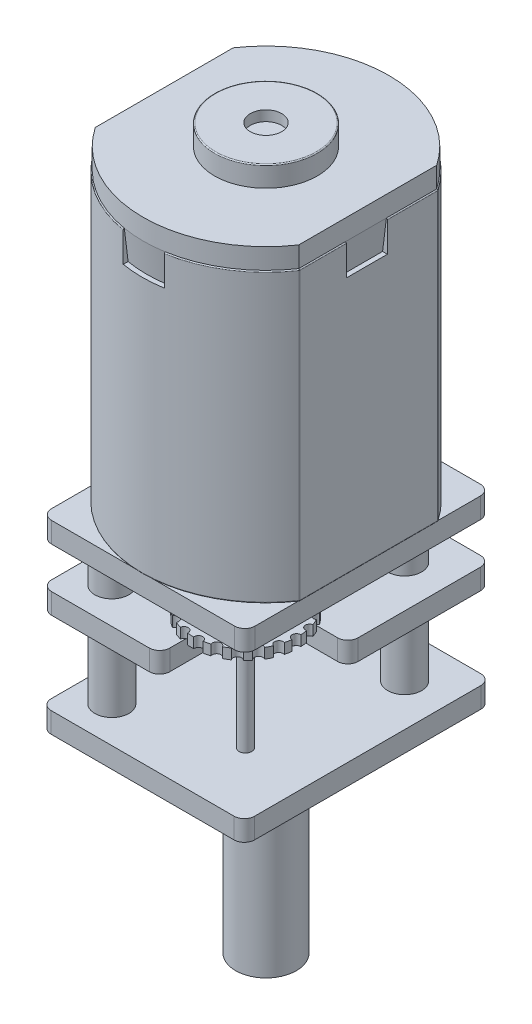
SolidWorks part; units mm, degrees
ref_plane "Front Plane" through (0, 0, 0) normal (0, 0, 1) x (1, 0, 0)
ref_plane "Top Plane" through (0, 0, 0) normal (0, 1, 0) x (1, 0, 0)
ref_plane "Right Plane" through (0, 0, 0) normal (1, 0, 0) x (0, 0, -1)
sketch "Sketch1" plane through (0, 0, 0) normal (0, 1, 0) x (1, 0, 0)
  line L2 (-5, -3.3706) -> (-5, 3.3706)
  line L4 (5, -3.3706) -> (5, 3.3706)
  line L5 (-3.051, -5.2012) -> (3.051, 5.2012) construction
  line L6 (-3.051, 5.2012) -> (3.051, -5.2012) construction
  arc A0 (-5, -3.3706) -> (5, -3.3706) centre (0, 0) ccw
  arc A1 (5, 3.3706) -> (-5, 3.3706) centre (0, 0) ccw
  dimension "D1" = 12.06
extrude "Boss-Extrude1" add sketch "Sketch1" along normal blind 14
fillet "Fillet2" radius 0.05 12 edges at (-5, 7, 3.3706) (5, 7, 3.3706) (5, 7, -3.3706) (-5, 7, -3.3706) (-5, 0, 0) (0, 0, -6.03) (5, 0, 0) (0, 0, 6.03) (-5, 14, 0) (0, 14, -6.03) (5, 14, 0) (0, 14, 6.03)
sketch "Sketch2" plane through (0, 14, 0) normal (0, 1, 0) x (1, 0, 0)
  line L1 (1, 7.8898) -> (-1, 7.8898)
  line L2 (1, 7.8898) -> (1, -7.8898)
  line L3 (1, -7.8898) -> (-1, -7.8898)
  line L4 (-1, 7.8898) -> (-1, -7.8898)
  line L5 (1, 7.8898) -> (-1, -7.8898) construction
  line L6 (1, -7.8898) -> (-1, 7.8898) construction
  line L7 (6.96, 0.9081) -> (0, 0.9081)
  line L8 (6.96, 0.9081) -> (6.96, -1.0919)
  line L9 (6.96, -1.0919) -> (0, -1.0919)
  line L10 (0, 0.9081) -> (0, -1.0919)
  line L11 (6.96, 0.9081) -> (0, -1.0919) construction
  line L12 (6.96, -1.0919) -> (0, 0.9081) construction
  point P0 (0, 0)
  point P6 (3.48, -0.0919)
  dimension "D1" = 2
  dimension "D2" = 2
extrude "Cut-Extrude1" cut sketch "Sketch2" against normal blind 1.5 contours L2 L3 L4 L1 | L7 L10 L9 L8
sketch "Sketch3" plane through (0, 14, 0) normal (0, 1, 0) x (1, 0, 0)
  line L0 (4.95, 3.3553) -> (4.95, -3.3553)
  line L1 (-4.95, 3.3553) -> (-4.95, -3.3553)
  arc A0 (4.95, -3.3553) -> (-4.95, -3.3553) centre (0, 0) cw
  arc A1 (4.95, 3.3553) -> (-4.95, 3.3553) centre (0, 0) ccw
extrude "Boss-Extrude2" add sketch "Sketch3" along normal blind 1 and the other way blind 1.5 draft 7
sketch "Sketch4" plane through (0, 15, 0) normal (0, 1, 0) x (1, 0, 0)
  circle A0 centre (0, 0) radius 2.5
  dimension "D1" = 5
extrude "Boss-Extrude3" add sketch "Sketch4" along normal blind 1
fillet "Fillet3" radius 0.05 1 edges at (0, 16, 2.5)
sketch "Sketch5" plane through (0, 16, 0) normal (0, 1, 0) x (1, 0, 0)
  circle A0 centre (0, 0) radius 0.7637
extrude "Cut-Extrude2" cut sketch "Sketch5" against normal blind 0.5
sketch "Sketch6" plane through (0, 0, 0) normal (0, -1, 0) x (-1, 0, 0)
  line L1 (-4.45, -5.98) -> (4.45, -5.98)
  line L2 (-4.95, -5.48) -> (-4.95, 5.48)
  line L3 (-4.45, 5.98) -> (4.45, 5.98)
  line L4 (4.95, -5.48) -> (4.95, 5.48)
  line L5 (-4.95, -5.98) -> (4.95, 5.98) construction
  line L6 (-4.95, 5.98) -> (4.95, -5.98) construction
  arc A0 (-4.95, 5.48) -> (-4.45, 5.98) centre (-4.45, 5.48) cw
  arc A1 (4.45, 5.98) -> (4.95, 5.48) centre (4.45, 5.48) cw
  arc A2 (4.45, -5.98) -> (4.95, -5.48) centre (4.45, -5.48) ccw
  arc A3 (-4.45, -5.98) -> (-4.95, -5.48) centre (-4.45, -5.48) cw
  point P0 (0, 0)
  dimension "D1" = 0.5
extrude "Boss-Extrude4" add sketch "Sketch6" along normal blind 1
sketch "Sketch7" plane through (0, -1, 0) normal (0, -1, 0) x (1, 0, 0)
  line L0 (-4.8036, -5.8336) -> (4.8036, 5.8336) construction
  circle A0 centre (2.8963, -3.8498) radius 0.8279
  arc A1 (-4.95, -5.48) -> (-4.45, -5.98) centre (-4.45, -5.48) ccw construction
  arc A2 (4.95, 5.48) -> (4.45, 5.98) centre (4.45, 5.48) ccw construction
  circle A3 centre (-3.2633, 4.2361) radius 0.8279
extrude "Boss-Extrude5" add sketch "Sketch7" along normal blind 2
sketch "Sketch8" plane through (0, -3, 0) normal (0, -1, 0) x (1, 0, 0)
  line L1 (0.2998, 5.98) -> (-4.45, 5.98)
  line L2 (4.95, 0.4662) -> (4.95, -5.48)
  line L3 (4.45, -5.98) -> (-4.45, -5.98)
  line L4 (-4.95, 5.48) -> (-4.95, -5.48)
  line L5 (0.7998, 0.9662) -> (-4.95, -5.98) construction
  line L6 (4.95, -5.98) -> (-4.95, 5.98) construction
  line L9 (4.45, 0.9662) -> (0.7998, 0.9662)
  line L10 (0.7998, 5.48) -> (0.7998, 0.9662)
  arc A0 (4.95, -5.48) -> (4.45, -5.98) centre (4.45, -5.48) cw
  arc A1 (-4.45, -5.98) -> (-4.95, -5.48) centre (-4.45, -5.48) cw
  arc A2 (-4.45, 5.98) -> (-4.95, 5.48) centre (-4.45, 5.48) ccw
  arc A4 (4.45, 0.9662) -> (4.95, 0.4662) centre (4.45, 0.4662) cw
  arc A5 (0.7998, 5.48) -> (0.2998, 5.98) centre (0.2998, 5.48) ccw
  point P0 (0, 0)
  point P18 (2.9985, 3.6225)
  dimension "D1" = 0.5
  dimension "D2" = 0.5
extrude "Boss-Extrude6" add sketch "Sketch8" along normal blind 1
sketch "Sketch9" plane through (0, -4, 0) normal (0, -1, 0) x (1, 0, 0)
  circle A0 centre (2.8963, -3.8498) radius 0.8279
  circle A1 centre (-3.2633, 4.2361) radius 0.8279
extrude "Boss-Extrude7" add sketch "Sketch9" along normal blind 4
sketch "Sketch10" plane through (0, -8, 0) normal (0, -1, 0) x (1, 0, 0)
  line L1 (-4.45, 6.0041) -> (4.45, 6.0041)
  line L2 (-4.95, 5.5041) -> (-4.95, -5.5041)
  line L3 (-4.45, -6.0041) -> (4.45, -6.0041)
  line L4 (4.95, 5.5041) -> (4.95, -5.5041)
  line L5 (-4.95, 6.0041) -> (4.95, -6.0041) construction
  line L6 (-4.95, -6.0041) -> (4.95, 6.0041) construction
  arc A0 (-4.45, 6.0041) -> (-4.95, 5.5041) centre (-4.45, 5.5041) ccw
  arc A1 (4.45, 6.0041) -> (4.95, 5.5041) centre (4.45, 5.5041) cw
  arc A2 (4.45, -6.0041) -> (4.95, -5.5041) centre (4.45, -5.5041) ccw
  arc A3 (-4.95, -5.5041) -> (-4.45, -6.0041) centre (-4.45, -5.5041) ccw
  point P0 (0, 0)
  dimension "D1" = 0.5
extrude "Boss-Extrude8" add sketch "Sketch10" along normal blind 1
sketch "Sketch11" plane through (0, -9, 0) normal (0, -1, 0) x (1, 0, 0)
  line L0 (0, 0) -> (-4.95, 0) construction
  line L1 (-4.95, 5.5041) -> (-4.95, -5.5041) construction
  circle A0 centre (0, -4.7025) radius 0.1889
  circle A1 centre (0, 4.7025) radius 0.1889
  circle A2 centre (2.8963, -3.8498) radius 1.0027
  circle A3 centre (-3.2633, 4.2361) radius 0.9932
extrude "Cut-Extrude3" cut sketch "Sketch11" against normal blind 0.07
sketch "Sketch13" plane through (0, -9, 0) normal (0, -1, 0) x (-1, 0, 0)
  line L0 (0, 0) -> (0, 3.5065) construction
  line L9 (0.93, 1.1513) -> (0.93, -1.1513)
  arc A0 (0.93, 1.1513) -> (0.93, -1.1513) centre (0, 0) ccw
  point P3 (0, 1.48)
  dimension "D1" = 2.96
  dimension "D2" = 0.93
extrude "Boss-Extrude9" add sketch "Sketch13" along normal blind 10
sketch "Sketch14" plane through (0, -9, 0) normal (0, -1, 0) x (1, 0, 0)
  circle A0 centre (0, 0) radius 2.02
  circle A1 centre (0, 0) radius 1.5749
  dimension "D1" = 4.04
extrude "Boss-Extrude10" add sketch "Sketch14" along normal blind 1
sketch "Sketch15" plane through (0, -4, 0) normal (0, -1, 0) x (1, 0, 0)
  arc A0 (0.4556, -1.9195) -> (0.3988, -1.6073) centre (-2.1098, -2.2253) ccw
  arc A1 (0.2137, -3.3551) -> (0, -3.7165) centre (0.1068, -3.5358) ccw
  arc A2 (-0.1987, -3.9639) -> (-0.5056, -4.2505) centre (-0.3522, -4.1072) ccw
  arc A3 (-0.766, -4.4319) -> (-1.1411, -4.6205) centre (-0.9536, -4.5262) ccw
  arc A4 (-1.4421, -4.7211) -> (-1.8552, -4.7963) centre (-1.6486, -4.7587) ccw
  arc A5 (-2.1723, -4.8082) -> (-2.5898, -4.7639) centre (-2.3811, -4.7861) ccw
  arc A6 (-2.8974, -4.6859) -> (-3.2856, -4.5259) centre (-3.0915, -4.6059) ccw
  arc A7 (-3.5588, -4.3644) -> (-3.8861, -4.1014) centre (-3.7225, -4.2329) ccw
  arc A8 (-4.1027, -3.8695) -> (-4.3428, -3.525) centre (-4.2227, -3.6972) ccw
  arc A9 (-4.4852, -3.2414) -> (-4.6185, -2.8432) centre (-4.5519, -3.0423) ccw
  arc A10 (-4.6753, -2.531) -> (-4.691, -2.1115) centre (-4.6831, -2.3212) ccw
  arc A11 (-4.6575, -1.7959) -> (-4.5543, -1.3889) centre (-4.6059, -1.5924) ccw
  arc A12 (-4.4333, -1.0955) -> (-4.2197, -0.7341) centre (-4.3265, -0.9148) ccw
  arc A13 (-4.0209, -0.4867) -> (-3.7141, -0.2001) centre (-3.8675, -0.3434) ccw
  arc A14 (-3.4537, -0.0187) -> (-3.0785, 0.1699) centre (-3.2661, 0.0756) ccw
  arc A15 (-2.7776, 0.2706) -> (-2.3645, 0.3458) centre (-2.571, 0.3082) ccw
  arc A16 (-2.0474, 0.3576) -> (-1.6298, 0.3134) centre (-1.8386, 0.3355) ccw
  arc A17 (-1.3222, 0.2354) -> (-0.934, 0.0753) centre (-1.1281, 0.1553) ccw
  arc A18 (-0.6609, -0.0862) -> (-0.3335, -0.3492) centre (-0.4972, -0.2177) ccw
  arc A19 (-0.1169, -0.5811) -> (0.1231, -0.9256) centre (0.0031, -0.7533) ccw
  arc A20 (0.2656, -1.2091) -> (0.3988, -1.6073) centre (0.3322, -1.4082) ccw
  arc A21 (0.4556, -1.9195) -> (0.4713, -2.3391) centre (0.4635, -2.1293) ccw
  arc A22 (0.4379, -2.6547) -> (0.3347, -3.0617) centre (0.3863, -2.8582) ccw
  arc A23 (0.4379, -2.6547) -> (0.4713, -2.3391) centre (-2.1098, -2.2253) ccw
  arc A24 (0.2137, -3.3551) -> (0.3347, -3.0617) centre (-2.1098, -2.2253) ccw
  arc A25 (-0.1987, -3.9639) -> (0, -3.7165) centre (-2.1098, -2.2253) ccw
  arc A26 (-0.766, -4.4319) -> (-0.5056, -4.2505) centre (-2.1098, -2.2253) ccw
  arc A27 (-1.4421, -4.7211) -> (-1.1411, -4.6205) centre (-2.1098, -2.2253) ccw
  arc A28 (-2.1723, -4.8082) -> (-1.8552, -4.7963) centre (-2.1098, -2.2253) ccw
  arc A29 (-2.8974, -4.6859) -> (-2.5898, -4.7639) centre (-2.1098, -2.2253) ccw
  arc A30 (-3.5588, -4.3644) -> (-3.2856, -4.5259) centre (-2.1098, -2.2253) ccw
  arc A31 (-4.1027, -3.8695) -> (-3.8861, -4.1014) centre (-2.1098, -2.2253) ccw
  arc A32 (-4.4852, -3.2414) -> (-4.3428, -3.525) centre (-2.1098, -2.2253) ccw
  arc A33 (-4.6753, -2.531) -> (-4.6185, -2.8432) centre (-2.1098, -2.2253) ccw
  arc A34 (-4.6575, -1.7959) -> (-4.691, -2.1115) centre (-2.1098, -2.2253) ccw
  arc A35 (-4.4333, -1.0955) -> (-4.5543, -1.3889) centre (-2.1098, -2.2253) ccw
  arc A36 (-4.0209, -0.4867) -> (-4.2197, -0.7341) centre (-2.1098, -2.2253) ccw
  arc A37 (-3.4537, -0.0187) -> (-3.7141, -0.2001) centre (-2.1098, -2.2253) ccw
  arc A38 (-2.7776, 0.2706) -> (-3.0785, 0.1699) centre (-2.1098, -2.2253) ccw
  arc A39 (-2.0474, 0.3576) -> (-2.3645, 0.3458) centre (-2.1098, -2.2253) ccw
  arc A40 (-1.3222, 0.2354) -> (-1.6298, 0.3134) centre (-2.1098, -2.2253) ccw
  arc A41 (-0.6609, -0.0862) -> (-0.934, 0.0753) centre (-2.1098, -2.2253) ccw
  arc A42 (-0.1169, -0.5811) -> (-0.3335, -0.3492) centre (-2.1098, -2.2253) ccw
  arc A43 (0.2656, -1.2091) -> (0.1231, -0.9256) centre (-2.1098, -2.2253) ccw
  point P70 (-2.1098, -2.2253)
  dimension "D1" = 22
extrude "Boss-Extrude11" add sketch "Sketch15" along normal blind 0.5 from offset 2 separate body contours A0 A20 A43 A19 A42 A18 A41 A17 A40 A16 A39 A15 A38 A14 A37 A13 A36 A12 A35 A11 A34 A10 A33 A9 A32 A8 A31 A7 A30 A6 A29 A5 A28 A4 A27 A3 A26 A2 A25 A1 A24 A22 A23 A21
sketch "Sketch16" plane through (0, -1, 0) normal (0, -1, 0) x (1, 0, 0)
  arc A0 (4.4137, 3.154) -> (4.3569, 3.4662) centre (1.8482, 2.8483) ccw
  arc A1 (4.1717, 1.7185) -> (3.958, 1.357) centre (4.0649, 1.5378) ccw
  arc A2 (3.7593, 1.1096) -> (3.4524, 0.823) centre (3.6059, 0.9663) ccw
  arc A3 (3.1921, 0.6416) -> (2.8169, 0.4531) centre (3.0045, 0.5474) ccw
  arc A4 (2.516, 0.3524) -> (2.1029, 0.2772) centre (2.3094, 0.3148) ccw
  arc A5 (1.7857, 0.2654) -> (1.3682, 0.3096) centre (1.577, 0.2875) ccw
  arc A6 (1.0606, 0.3876) -> (0.6724, 0.5477) centre (0.8665, 0.4677) ccw
  arc A7 (0.3993, 0.7092) -> (0.0719, 0.9721) centre (0.2356, 0.8407) ccw
  arc A8 (-0.1447, 1.2041) -> (-0.3847, 1.5486) centre (-0.2647, 1.3763) ccw
  arc A9 (-0.5272, 1.8321) -> (-0.6604, 2.2303) centre (-0.5938, 2.0312) ccw
  arc A10 (-0.7173, 2.5425) -> (-0.7329, 2.9621) centre (-0.7251, 2.7523) ccw
  arc A11 (-0.6995, 3.2777) -> (-0.5963, 3.6847) centre (-0.6479, 3.4812) ccw
  arc A12 (-0.4753, 3.9781) -> (-0.2616, 4.3395) centre (-0.3685, 4.1588) ccw
  arc A13 (-0.0629, 4.5869) -> (0.244, 4.8735) centre (0.0905, 4.7302) ccw
  arc A14 (0.5044, 5.0549) -> (0.8795, 5.2434) centre (0.6919, 5.1492) ccw
  arc A15 (1.1805, 5.3441) -> (1.5936, 5.4193) centre (1.387, 5.3817) ccw
  arc A16 (1.9107, 5.4311) -> (2.3282, 5.3869) centre (2.1194, 5.409) ccw
  arc A17 (2.6358, 5.3089) -> (3.024, 5.1488) centre (2.8299, 5.2289) ccw
  arc A18 (3.2972, 4.9874) -> (3.6245, 4.7244) centre (3.4608, 4.8559) ccw
  arc A19 (3.8411, 4.4925) -> (4.0811, 4.148) centre (3.9611, 4.3202) ccw
  arc A20 (4.2236, 3.8644) -> (4.3569, 3.4662) centre (4.2902, 3.6653) ccw
  arc A21 (4.4137, 3.154) -> (4.4293, 2.7344) centre (4.4215, 2.9442) ccw
  arc A22 (4.3959, 2.4189) -> (4.2927, 2.0119) centre (4.3443, 2.2154) ccw
  arc A23 (4.3959, 2.4189) -> (4.4293, 2.7344) centre (1.8482, 2.8483) ccw
  arc A24 (4.1717, 1.7185) -> (4.2927, 2.0119) centre (1.8482, 2.8483) ccw
  arc A25 (3.7593, 1.1096) -> (3.958, 1.357) centre (1.8482, 2.8483) ccw
  arc A26 (3.1921, 0.6416) -> (3.4524, 0.823) centre (1.8482, 2.8483) ccw
  arc A27 (2.516, 0.3524) -> (2.8169, 0.4531) centre (1.8482, 2.8483) ccw
  arc A28 (1.7857, 0.2654) -> (2.1029, 0.2772) centre (1.8482, 2.8483) ccw
  arc A29 (1.0606, 0.3876) -> (1.3682, 0.3096) centre (1.8482, 2.8483) ccw
  arc A30 (0.3993, 0.7092) -> (0.6724, 0.5477) centre (1.8482, 2.8483) ccw
  arc A31 (-0.1447, 1.2041) -> (0.0719, 0.9721) centre (1.8482, 2.8483) ccw
  arc A32 (-0.5272, 1.8321) -> (-0.3847, 1.5486) centre (1.8482, 2.8483) ccw
  arc A33 (-0.7173, 2.5425) -> (-0.6604, 2.2303) centre (1.8482, 2.8483) ccw
  arc A34 (-0.6995, 3.2777) -> (-0.7329, 2.9621) centre (1.8482, 2.8483) ccw
  arc A35 (-0.4753, 3.9781) -> (-0.5963, 3.6847) centre (1.8482, 2.8483) ccw
  arc A36 (-0.0629, 4.5869) -> (-0.2616, 4.3395) centre (1.8482, 2.8483) ccw
  arc A37 (0.5044, 5.0549) -> (0.244, 4.8735) centre (1.8482, 2.8483) ccw
  arc A38 (1.1805, 5.3441) -> (0.8795, 5.2434) centre (1.8482, 2.8483) ccw
  arc A39 (1.9107, 5.4311) -> (1.5936, 5.4193) centre (1.8482, 2.8483) ccw
  arc A40 (2.6358, 5.3089) -> (2.3282, 5.3869) centre (1.8482, 2.8483) ccw
  arc A41 (3.2972, 4.9874) -> (3.024, 5.1488) centre (1.8482, 2.8483) ccw
  arc A42 (3.8411, 4.4925) -> (3.6245, 4.7244) centre (1.8482, 2.8483) ccw
  arc A43 (4.2236, 3.8644) -> (4.0811, 4.148) centre (1.8482, 2.8483) ccw
extrude "Boss-Extrude12" add sketch "Sketch16" along normal blind 0.5 from offset 1 separate body
sketch "Sketch17" plane through (0, -4, 0) normal (0, -1, 0) x (1, 0, 0)
  circle A0 centre (-2.1098, -2.2253) radius 0.3105
extrude "Boss-Extrude13" add sketch "Sketch17" along normal up to surface and the other way up to surface
sketch "Sketch18" plane through (0, -1, 0) normal (0, -1, 0) x (-1, 0, 0)
  circle A0 centre (-1.8482, -2.8483) radius 0.309
extrude "Boss-Extrude14" add sketch "Sketch18" along normal up to surface (7 mm away) up to face at (-2.1098, -8, -2.5358)
